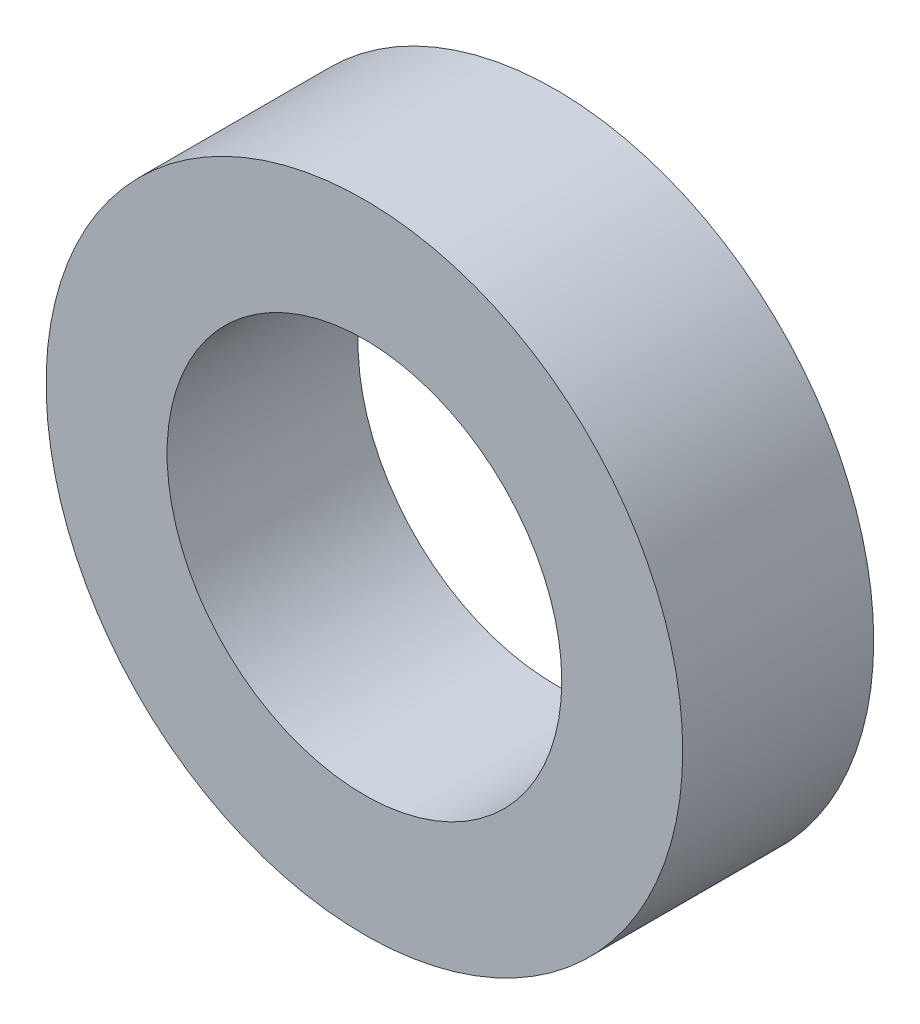
SolidWorks part; units mm, degrees
ref_plane "正面" through (0, 0, 0) normal (0, 0, 1) x (1, 0, 0)
ref_plane "平面" through (0, 0, 0) normal (0, 1, 0) x (1, 0, 0)
ref_plane "右側面" through (0, 0, 0) normal (1, 0, 0) x (0, 0, -1)
sketch "ｽｹｯﾁ1" plane through (0, 0, 0) normal (0, 0, 1) x (1, 0, 0)
  circle A0 centre (0, 0) radius 3.1
  circle A1 centre (0, 0) radius 5
  dimension "D1" = 6.2
  dimension "D2" = 10
extrude "ﾎﾞｽ - 押し出し1" add sketch "ｽｹｯﾁ1" along normal blind 3
